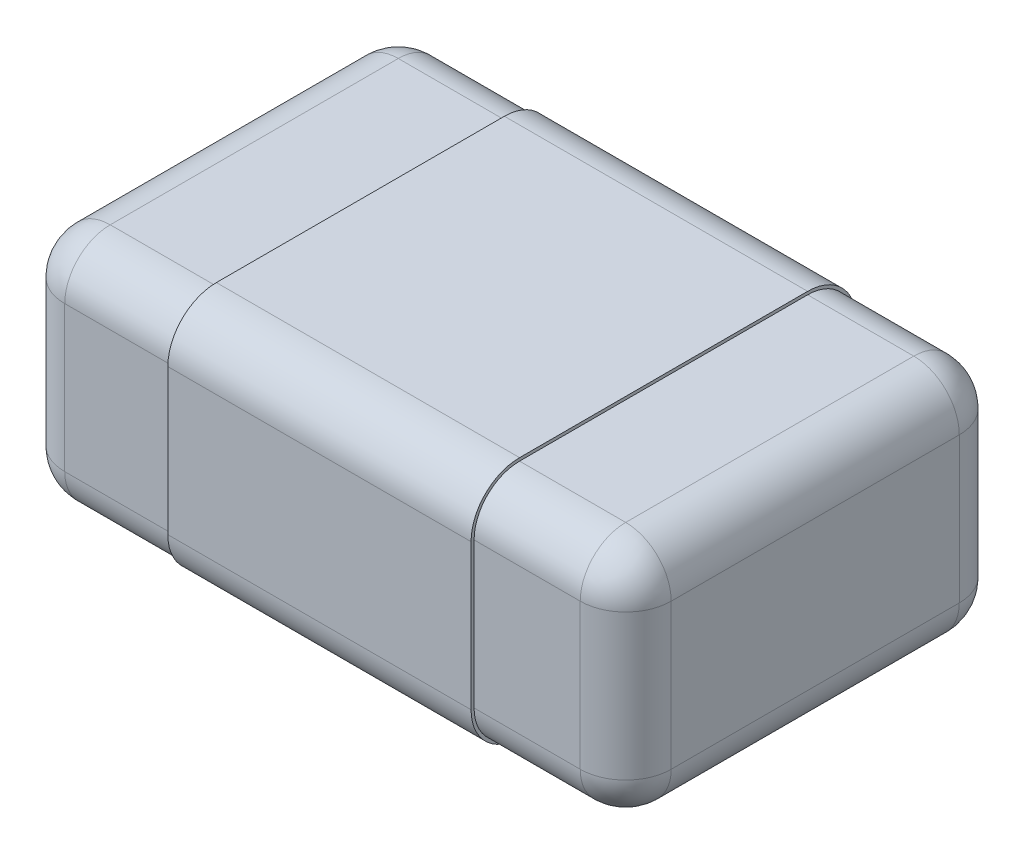
SolidWorks part; units mm, degrees
material "Aço inoxidável fundido"
ref_plane "Plano frontal" through (0, 0, 0) normal (0, 0, 1) x (1, 0, 0)
ref_plane "Plano superior" through (0, 0, 0) normal (0, 1, 0) x (1, 0, 0)
ref_plane "Plano direito" through (0, 0, 0) normal (1, 0, 0) x (0, 0, -1)
sketch "Esboço1" plane through (0, 0, 0) normal (0, 1, 0) x (1, 0, 0)
  line L0 (-1, -0.625) -> (1, -0.625)
  line L1 (1, -0.625) -> (1, 0.625)
  line L2 (1, 0.625) -> (-1, 0.625)
  line L3 (-1, 0.625) -> (-1, -0.625)
extrude "Ressalto-extrusão1" add sketch "Esboço1" against normal blind 0.78
fillet "Filete1" radius 0.15 12 edges at (0, -0.78, -0.625) (-1, -0.39, -0.625) (1, -0.39, -0.625) (0, 0, -0.625) (-1, -0.78, 0) (1, -0.78, 0) (0, -0.78, 0.625) (-1, 0, 0) (1, 0, 0) (-1, -0.39, 0.625) (1, -0.39, 0.625) (0, 0, 0.625)
sketch "Esboço4" plane through (0, 0, 0) normal (1, 0, 0) x (0, 0, -1)
  line L0 (0.625, -0.63) -> (0.625, -0.15) construction
  line L1 (0.625, -0.63) -> (0.625, -0.15)
  line L2 (0.475, -0.78) -> (-0.475, -0.78) construction
  line L3 (0.475, -0.78) -> (-0.475, -0.78)
  line L4 (0.475, 0) -> (-0.475, 0) construction
  line L5 (-0.625, -0.15) -> (-0.625, -0.63) construction
  line L6 (0.475, 0) -> (-0.475, 0)
  line L7 (-0.625, -0.15) -> (-0.625, -0.63)
  line L8 (0.635, -0.63) -> (0.635, -0.15)
  line L9 (0.475, 0.01) -> (-0.475, 0.01)
  line L10 (-0.635, -0.15) -> (-0.635, -0.63)
  line L11 (0.475, -0.79) -> (-0.475, -0.79)
  arc A5 (0.475, -0.78) -> (0.625, -0.63) centre (0.475, -0.63) ccw construction
  arc A6 (0.475, -0.78) -> (0.625, -0.63) centre (0.475, -0.63) ccw
  arc A7 (-0.475, 0) -> (-0.625, -0.15) centre (-0.475, -0.15) ccw construction
  arc A8 (-0.625, -0.63) -> (-0.475, -0.78) centre (-0.475, -0.63) ccw construction
  arc A9 (-0.475, 0) -> (-0.625, -0.15) centre (-0.475, -0.15) ccw
  arc A10 (-0.625, -0.63) -> (-0.475, -0.78) centre (-0.475, -0.63) ccw
  arc A11 (0.625, -0.15) -> (0.475, 0) centre (0.475, -0.15) ccw construction
  arc A12 (0.625, -0.15) -> (0.475, 0) centre (0.475, -0.15) ccw
  arc A13 (0.635, -0.15) -> (0.475, 0.01) centre (0.475, -0.15) ccw
  arc A14 (-0.475, 0.01) -> (-0.635, -0.15) centre (-0.475, -0.15) ccw
  arc A15 (-0.635, -0.63) -> (-0.475, -0.79) centre (-0.475, -0.63) ccw
  arc A16 (0.475, -0.79) -> (0.635, -0.63) centre (0.475, -0.63) ccw
  dimension "D1" = 0.01
extrude "Ressalto-extrusão4" add sketch "Esboço4" along normal blind 0.5 and the other way blind 0.5
sketch "Esboço2" plane through (0, -0.79, 0) normal (0, -1, 0) x (0, 0, 1)
  line L1 (-0.475, 0.5) -> (0.475, 0.5) construction
  line L2 (-0.475, -0.5) -> (0.475, -0.5) construction
  line L7 (0.2404, -0.5) -> (0.2404, 0.5) construction
  text T0 "<b>203</b>\r\n" font "Tahoma" height 0.5
extrude "Ressalto-extrusão5" add sketch "Esboço2" along normal blind 0.02
